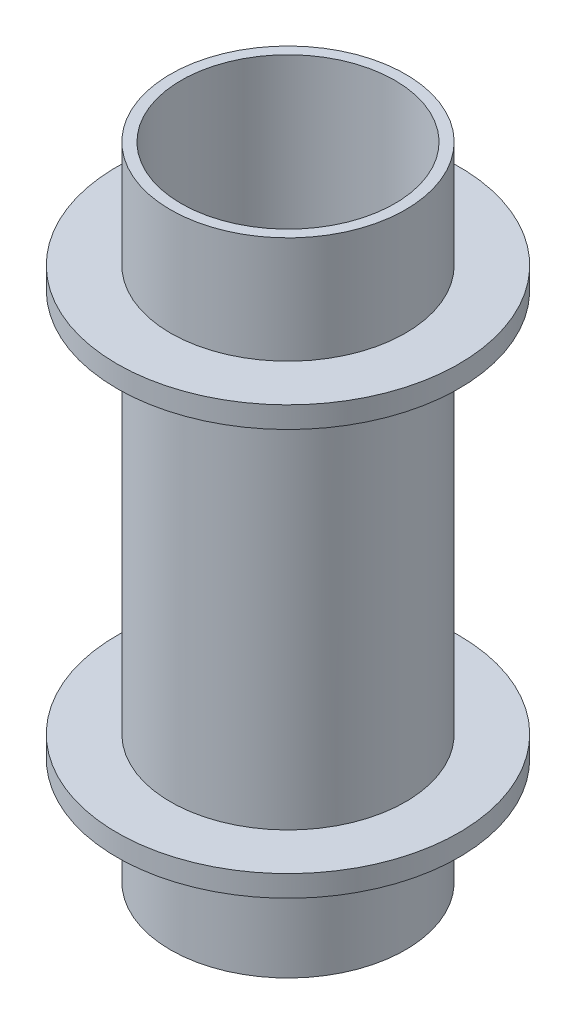
SolidWorks part; units mm, degrees
ref_plane "Спереди" through (0, 0, 0) normal (0, 0, 1) x (1, 0, 0)
ref_plane "Сверху" through (0, 0, 0) normal (0, 1, 0) x (1, 0, 0)
ref_plane "Справа" through (0, 0, 0) normal (1, 0, 0) x (0, 0, -1)
other "Центр тяжести"
sketch "Эскиз1" plane through (0, 0, 0) normal (0, 1, 0) x (1, 0, 0)
  circle A0 centre (0, 0) radius 10
  circle A1 centre (0, 0) radius 11
  dimension "D1" = 20
  dimension "D2" = 22
extrude "Бобышка-Вытянуть1" add sketch "Эскиз1" along normal blind 60
sketch "Эскиз2" plane through (0, 60, 0) normal (0, 1, 0) x (1, 0, 0)
  circle A1 centre (0, 0) radius 16
  circle A3 centre (0, 0) radius 11
  dimension "D1" = 32
  dimension "D2" = 22
extrude "Бобышка-Вытянуть3" add sketch "Эскиз2" against normal blind 2 from offset 10 offset against normal yes
sketch "Эскиз3" plane through (0, 0, 0) normal (0, -1, 0) x (1, 0, 0)
  circle A0 centre (0, 0) radius 11
  circle A1 centre (0, 0) radius 16
  dimension "D1" = 22
extrude "Бобышка-Вытянуть4" add sketch "Эскиз3" against normal blind 2 from offset 10
